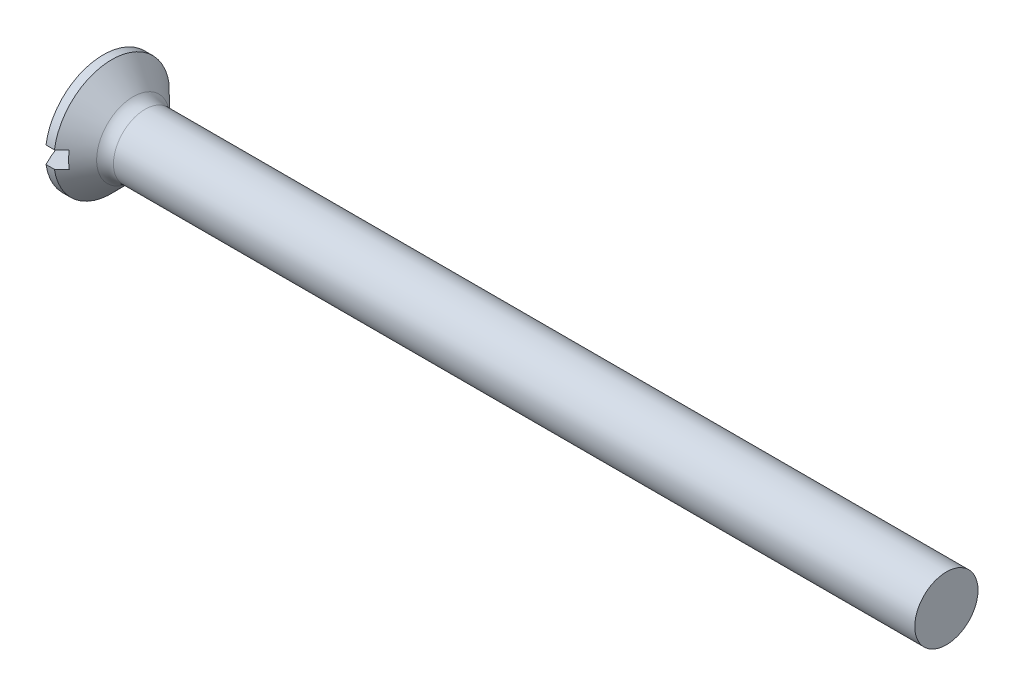
SolidWorks part; units mm, degrees
ref_plane "Plane1" through (0, 0, 0) normal (0, 0, 1) x (1, 0, 0)
ref_plane "Plane2" through (0, 0, 0) normal (0, 1, 0) x (1, 0, 0)
ref_plane "Plane3" through (0, 0, 0) normal (1, 0, 0) x (0, 0, -1)
sketch "BodySke" plane through (0, 0, 0) normal (0, 0, 1) x (1, 0, 0)
  line L0 (0, 0) -> (30.7, 0)
  line L1 (30.7, 0) -> (30.7, 1.5)
  line L2 (30.7, 1.5) -> (2.35, 1.5)
  line L3 (1.1, -2.75) -> (2.35, -1.5) construction
  line L4 (-15.875, 0) -> (82.55, 0) construction
  line L5 (1.1, 2.75) -> (2.35, 1.5)
  line L6 (2.85, 4.675) -> (2.85, -11.2) construction
  line L7 (0.7, 2.7793) -> (0.7, -13.0957) construction
  line L8 (1.1, 2.75) -> (0.7, 2.75)
  arc A0 (0, 0) -> (0.7, 2.75) centre (5.7518, 0) cw
  dimension "Length" = 30
  dimension "Diameter" = 3
  dimension "Head_dia" = 5.5
  dimension "Head_ang" = 90
  dimension "Advance" = 0.5
  dimension "Thread_nom" = 30
  dimension "Oval_ht" = 0.7
  dimension "Side_ht" = 1.65
revolve "Base-Revolve" add sketch "BodySke"
cosmetic thread "ThreadCosmetic" [suppressed]
extrude "Slot" cut sketch "Sketch2" along normal blind 1.45
sketch "Sketch2" plane through (0, 0, 0) normal (1, 0, 0) x (0, 0, -1)
  line L0 (2.75, -0.4) -> (-2.75, -0.4)
  line L1 (2.75, -0.4) -> (2.75, 0.4)
  line L2 (-2.75, 0.4) -> (2.75, 0.4)
  line L3 (-2.75, 0.4) -> (-2.75, -0.4)
  dimension "D1" = 5.5
  dimension "Slot_width" = 0.8
  dimension "D3" = 2.75
  dimension "D4" = 0.4
fillet "Fillet1" radius 0.8 1 edges at (2.35, 0, 1.5)
sketch "ThdSchSke" plane through (0, 0, 0) normal (0, 0, 1) x (1, 0, 0)
  line L0 (2.85, -1.2195) -> (2.6536, -1.5)
  line L1 (2.85, -1.2195) -> (3.0464, -1.5)
  line L2 (3.0464, -1.5) -> (3.0464, -1.875)
  line L3 (-3.175, 0) -> (5.1513, 0) construction
  line L5 (3.0464, -1.875) -> (2.6536, -1.875)
  line L6 (2.6536, -1.875) -> (2.6536, -1.5)
  dimension "Thread_minor" = 2.439
  dimension "Diameter" = 3
  dimension "Start" = 2.85
  dimension "SideAngle" = 55
  dimension "VeeAngle" = 70
  dimension "Overcut" = 3.75
revolve "ThreadSchematic" [suppressed] cut sketch "ThdSchSke" angle 360 about L3
pattern_linear "ThdSchPat" [suppressed]
sketch "Esboço1" plane through (30.7, 0, 0) normal (1, 0, 0) x (0, 0, -1)
  circle A0 centre (0, 0) radius 1.5
extrude "Ressalto-extrusão1" add sketch "Esboço1" along normal blind 10
equation "\"D1@Sketch2\" = \"Head_dia@BodySke\""
equation "\"D3@Sketch2\" = \"D1@Sketch2\" / 2"
equation "\"D4@Sketch2\" = \"Slot_width@Sketch2\" / 2"
equation "\"Thread_length@ThreadCosmetic\" = ((sgn( (\"Length@BodySke\" - \"Advance@BodySke\" - \"Side_ht@BodySke\" ) - \"Thread_nom@BodySke\" )-1)*( (\"Length@BodySke\" - \"Advance@BodySke\" - \"Side_ht@BodySke\" ) - \"Thread_nom@BodySke\" ))/-2+ \"Thread_nom@BodySke\""
equation "\"Thread_minor@ThdSchSke\" = \"Thread_minor@ThreadCosmetic\""
equation "\"Diameter@ThdSchSke\" = \"Diameter@BodySke\""
equation "\"Overcut@ThdSchSke\" = \"Diameter@BodySke\" * 1.25"
equation "\"Start@ThdSchSke\" = \"Oval_ht@BodySke\" + \"Length@BodySke\" - \"Thread_length@ThreadCosmetic\"  '---Countersunk---"
equation "\"Num_threads@ThdSchPat\" = int( \"Thread_length@ThreadCosmetic\" / \"Advance@BodySke\" + 0.999 )  + 1"
equation "\"Advance@ThdSchPat\" = \"Thread_length@ThreadCosmetic\" /  (\"Num_threads@ThdSchPat\" - 1) 'relax it"
